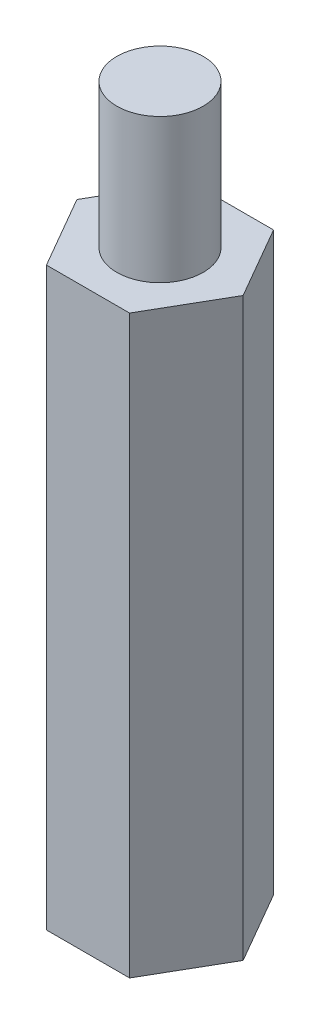
SolidWorks part; units mm, degrees
ref_plane "Front" through (0, 0, 0) normal (0, 0, 1) x (1, 0, 0)
ref_plane "Top" through (0, 0, 0) normal (0, 1, 0) x (1, 0, 0)
ref_plane "Right" through (0, 0, 0) normal (1, 0, 0) x (0, 0, -1)
sketch "草圖1" plane through (0, 0, 0) normal (0, 1, 0) x (1, 0, 0)
  line L1 (2.8868, 0) -> (1.4434, 2.5)
  line L2 (1.4434, 2.5) -> (-1.4434, 2.5)
  line L3 (-1.4434, 2.5) -> (-2.8868, 0)
  line L4 (-2.8868, 0) -> (-1.4434, -2.5)
  line L5 (-1.4434, -2.5) -> (1.4434, -2.5)
  line L6 (1.4434, -2.5) -> (2.8868, 0)
  circle A0 centre (0, 0) radius 2.5 construction
  dimension "D1" = 5
extrude "填料-伸長1" add sketch "草圖1" along normal blind 20
sketch "草圖2" plane through (0, 20, 0) normal (0, 1, 0) x (1, 0, 0)
  circle A0 centre (0, 0) radius 1.5
  dimension "D1" = 3
extrude "填料-伸長2" add sketch "草圖2" along normal blind 5
sketch "草圖3" plane through (0, 0, 0) normal (0, -1, 0) x (1, 0, 0)
  circle A0 centre (0, 0) radius 1.5
  dimension "D1" = 3
extrude "除料-伸長1" cut sketch "草圖3" against normal blind 5
